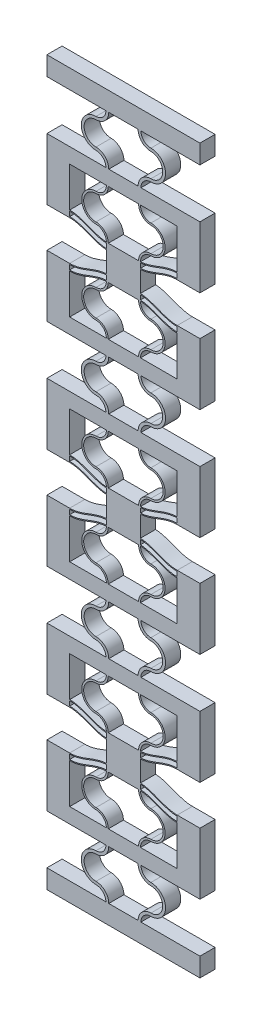
SolidWorks part; units mm, degrees
material "ABS"
ref_plane "Front Plane" through (0, 0, 0) normal (0, 0, 1) x (1, 0, 0)
ref_plane "Top Plane" through (0, 0, 0) normal (0, 1, 0) x (1, 0, 0)
ref_plane "Right Plane" through (0, 0, 0) normal (1, 0, 0) x (0, 0, -1)
sketch "Sketch1" plane through (0, 0, 0) normal (0, 0, 1) x (1, 0, 0)
  line L4 (0, 10.5) -> (0, 0)
  line L5 (10.2, 0) -> (10.2, 13) construction
  line L6 (10.2, 13) -> (10.2, 15.9852) construction
  line L17 (9.7, 0) -> (0, 0)
  line L18 (10.7, 0) -> (20.4, 0)
  line L19 (20.4, 0) -> (20.4, 10.5)
  line L20 (10.7, 13.2452) -> (10.7, 14.4852)
  line L21 (9.7, 13.2452) -> (9.7, 14.4852)
  line L22 (10.7, 14.7452) -> (10.7, 15.9852)
  line L23 (10.7, 15.9852) -> (9.7, 15.9852)
  line L24 (9.7, 15.9852) -> (9.7, 14.7452)
  line L31 (-5, 12.26) -> (-5, -4)
  line L32 (-5, -4) -> (25.4, -4)
  line L33 (25.4, -4) -> (25.4, 12.26)
  line L34 (0, 10.76) -> (0, 12)
  line L36 (-5, 12.26) -> (0, 12.26)
  line L37 (25.4, 12.26) -> (20.4, 12.26)
  line L38 (20.4, 10.76) -> (20.4, 12)
  arc A0 (10.2, 13) -> (6.95, 9.75) centre (6.95, 13) cw
  arc A1 (6.95, 9.75) -> (6.95, 3.25) centre (6.95, 6.5) ccw
  arc A2 (6.95, 3.25) -> (10.2, 0) centre (6.95, 0) cw
  arc A3 (9.7, 12.9852) -> (6.95, 10.25) centre (6.95, 13) cw
  arc A4 (6.95, 10.25) -> (6.95, 2.75) centre (6.95, 6.5) ccw
  arc A5 (6.95, 2.75) -> (9.7, 0) centre (6.95, 0) cw
  arc A6 (9.7, 13) -> (6.95, 10.25) centre (6.95, 13) cw construction
  arc A7 (13.45, 3.25) -> (10.2, 0) centre (13.45, 0) ccw
  arc A8 (13.45, 2.75) -> (10.7, 0) centre (13.45, 0) ccw
  arc A9 (13.45, 9.75) -> (13.45, 3.25) centre (13.45, 6.5) cw
  arc A10 (13.45, 10.25) -> (13.45, 2.75) centre (13.45, 6.5) cw
  arc A11 (10.7, 12.9852) -> (13.45, 10.25) centre (13.45, 13) ccw
  arc A12 (10.2, 13) -> (13.45, 9.75) centre (13.45, 13) ccw
  spline S0 degree 4 poles (-2.0399, 10.9987) (-1.9769, 10.9844) (-1.8506, 10.9568) (-1.6594, 10.9185) (-1.4063, 10.8738) (-1.1473, 10.836) (-0.8994, 10.8056) (-0.6275, 10.7825) (-0.4084, 10.7671) (-0.0945, 10.7598) (0.0489, 10.7593) (0.3554, 10.7653) (0.5833, 10.7785) (0.8327, 10.7992) (1.1232, 10.8326) (1.4148, 10.8743) (1.7521, 10.9345) (2.2064, 11.0333) (2.726, 11.1697) (3.2397, 11.3281) (3.7479, 11.5024) (4.1845, 11.6613) (4.5513, 11.7992) (4.9172, 11.9395) (5.2828, 12.0805) (5.7402, 12.2559) (6.427, 12.5125) (7.2136, 12.7819) (8.1107, 13.0284) (9.0261, 13.1932) (9.8075, 13.2661) (10.5925, 13.2661) (11.3739, 13.1932) (12.2893, 13.0284) (13.1864, 12.7819) (13.973, 12.5125) (14.6598, 12.2559) (15.2087, 12.0455) (15.6656, 11.8688) (16.1235, 11.6948) (16.6521, 11.5024) (17.1603, 11.3281) (17.6739, 11.1697) (18.1937, 11.0333) (18.5999, 10.9449) (18.8889, 10.8915) (19.1309, 10.8534) (19.3251, 10.827) (19.5196, 10.8048) (19.7158, 10.7868) (19.909, 10.7733) (20.1017, 10.7642) (20.3513, 10.7593) (20.4943, 10.7598) (20.8085, 10.7671) (21.0274, 10.7825) (21.2994, 10.8056) (21.5473, 10.836) (21.8063, 10.8738) (22.0594, 10.9185) (22.2506, 10.9568) (22.3769, 10.9844) (22.4399, 10.9987) knots 0 0 0 0 0 0.010251 0.020502 0.030753 0.041005 0.05113 0.061255 0.071381 0.081506 0.089265 0.097024 0.112543 0.120302 0.128061 0.143579 0.159098 0.174616 0.201648 0.22868 0.244198 0.259716 0.275235 0.290753 0.306271 0.32179 0.352826 0.40689 0.437927 0.468963 0.5 0.531037 0.562073 0.59311 0.647174 0.67821 0.693729 0.709247 0.740284 0.755802 0.77132 0.798352 0.825384 0.840902 0.856421 0.86418 0.871939 0.879698 0.887457 0.895217 0.902976 0.910735 0.918494 0.928619 0.938745 0.94887 0.958995 0.969247 0.979498 0.989749 1 1 1 1 1 construction
  spline S1 degree 4 poles (0, 10.76) (0.041, 10.76) (0.1243, 10.7608) (0.3554, 10.7653) (0.5833, 10.7785) (0.8327, 10.7992) (1.1232, 10.8326) (1.4148, 10.8743) (1.7521, 10.9345) (2.2064, 11.0333) (2.726, 11.1697) (3.2397, 11.3281) (3.7479, 11.5024) (4.1845, 11.6613) (4.5513, 11.7992) (4.9172, 11.9395) (5.2828, 12.0805) (5.7402, 12.2559) (6.427, 12.5125) (7.2136, 12.7819) (8.1107, 13.0284) (9.0261, 13.1932) (9.8075, 13.2661) (10.5925, 13.2661) (11.3739, 13.1932) (12.2893, 13.0284) (13.1864, 12.7819) (13.973, 12.5125) (14.6598, 12.2559) (15.2087, 12.0455) (15.6656, 11.8688) (16.1235, 11.6948) (16.6521, 11.5024) (17.1603, 11.3281) (17.6739, 11.1697) (18.1937, 11.0333) (18.5999, 10.9449) (18.8889, 10.8915) (19.1309, 10.8534) (19.3251, 10.827) (19.5196, 10.8048) (19.7158, 10.7868) (19.909, 10.7733) (20.1017, 10.7642) (20.2757, 10.7608) (20.359, 10.76) (20.4, 10.76) knots 0.081506 0.081506 0.081506 0.081506 0.081506 0.089265 0.097024 0.112543 0.120302 0.128061 0.143579 0.159098 0.174616 0.201648 0.22868 0.244198 0.259716 0.275235 0.290753 0.306271 0.32179 0.352826 0.40689 0.437927 0.468963 0.5 0.531037 0.562073 0.59311 0.647174 0.67821 0.693729 0.709247 0.740284 0.755802 0.77132 0.798352 0.825384 0.840902 0.856421 0.86418 0.871939 0.879698 0.887457 0.895217 0.902976 0.910735 0.918494 0.918494 0.918494 0.918494 0.918494
  spline S2 degree 4 poles (-2.0399, 12.2387) (-1.9769, 12.2244) (-1.8506, 12.1968) (-1.6594, 12.1585) (-1.4063, 12.1138) (-1.1473, 12.076) (-0.8994, 12.0456) (-0.6275, 12.0225) (-0.4084, 12.0071) (-0.0945, 11.9998) (0.0489, 11.9993) (0.3554, 12.0053) (0.5833, 12.0185) (0.8327, 12.0392) (1.1232, 12.0726) (1.4148, 12.1143) (1.7521, 12.1745) (2.2064, 12.2733) (2.726, 12.4097) (3.2397, 12.5681) (3.7479, 12.7424) (4.1845, 12.9013) (4.5513, 13.0392) (4.9172, 13.1795) (5.2828, 13.3205) (5.7402, 13.4959) (6.427, 13.7525) (7.2136, 14.0219) (8.1107, 14.2684) (9.0261, 14.4332) (9.8075, 14.5061) (10.5925, 14.5061) (11.3739, 14.4332) (12.2893, 14.2684) (13.1864, 14.0219) (13.973, 13.7525) (14.6598, 13.4959) (15.2087, 13.2855) (15.6656, 13.1088) (16.1235, 12.9348) (16.6521, 12.7424) (17.1603, 12.5681) (17.6739, 12.4097) (18.1937, 12.2733) (18.5999, 12.1849) (18.8889, 12.1315) (19.1309, 12.0934) (19.3251, 12.067) (19.5196, 12.0448) (19.7158, 12.0268) (19.909, 12.0133) (20.1017, 12.0042) (20.3513, 11.9993) (20.4943, 11.9998) (20.8085, 12.0071) (21.0274, 12.0225) (21.2994, 12.0456) (21.5473, 12.076) (21.8063, 12.1138) (22.0594, 12.1585) (22.2506, 12.1968) (22.3769, 12.2244) (22.4399, 12.2387) knots 0 0 0 0 0 0.010251 0.020502 0.030753 0.041005 0.05113 0.061255 0.071381 0.081506 0.089265 0.097024 0.112543 0.120302 0.128061 0.143579 0.159098 0.174616 0.201648 0.22868 0.244198 0.259716 0.275235 0.290753 0.306271 0.32179 0.352826 0.40689 0.437927 0.468963 0.5 0.531037 0.562073 0.59311 0.647174 0.67821 0.693729 0.709247 0.740284 0.755802 0.77132 0.798352 0.825384 0.840902 0.856421 0.86418 0.871939 0.879698 0.887457 0.895217 0.902976 0.910735 0.918494 0.928619 0.938745 0.94887 0.958995 0.969247 0.979498 0.989749 1 1 1 1 1 construction
  spline S3 degree 4 poles (0, 12) (0.041, 12) (0.1243, 12.0008) (0.3554, 12.0053) (0.5833, 12.0185) (0.8327, 12.0392) (1.1232, 12.0726) (1.4148, 12.1143) (1.7521, 12.1745) (2.2064, 12.2733) (2.726, 12.4097) (3.2397, 12.5681) (3.7479, 12.7424) (4.1845, 12.9013) (4.5513, 13.0392) (4.9172, 13.1795) (5.2828, 13.3205) (5.7402, 13.4959) (6.427, 13.7525) (7.2136, 14.0219) (8.1107, 14.2684) (9.0261, 14.4332) (9.8075, 14.5061) (10.5925, 14.5061) (11.3739, 14.4332) (12.2893, 14.2684) (13.1864, 14.0219) (13.973, 13.7525) (14.6598, 13.4959) (15.2087, 13.2855) (15.6656, 13.1088) (16.1235, 12.9348) (16.6521, 12.7424) (17.1603, 12.5681) (17.6739, 12.4097) (18.1937, 12.2733) (18.5999, 12.1849) (18.8889, 12.1315) (19.1309, 12.0934) (19.3251, 12.067) (19.5196, 12.0448) (19.7158, 12.0268) (19.909, 12.0133) (20.1017, 12.0042) (20.2757, 12.0008) (20.359, 12) (20.4, 12) knots 0.081506 0.081506 0.081506 0.081506 0.081506 0.089265 0.097024 0.112543 0.120302 0.128061 0.143579 0.159098 0.174616 0.201648 0.22868 0.244198 0.259716 0.275235 0.290753 0.306271 0.32179 0.352826 0.40689 0.437927 0.468963 0.5 0.531037 0.562073 0.59311 0.647174 0.67821 0.693729 0.709247 0.740284 0.755802 0.77132 0.798352 0.825384 0.840902 0.856421 0.86418 0.871939 0.879698 0.887457 0.895217 0.902976 0.910735 0.918494 0.918494 0.918494 0.918494 0.918494
  spline S4 degree 4 poles (-2.0399, 12.4987) (-1.9769, 12.4844) (-1.8506, 12.4568) (-1.6594, 12.4185) (-1.4063, 12.3738) (-1.1473, 12.336) (-0.8994, 12.3056) (-0.6275, 12.2825) (-0.4084, 12.2671) (-0.0945, 12.2598) (0.0489, 12.2593) (0.3554, 12.2653) (0.5833, 12.2785) (0.8327, 12.2992) (1.1232, 12.3326) (1.4148, 12.3743) (1.7521, 12.4345) (2.2064, 12.5333) (2.726, 12.6697) (3.2397, 12.8281) (3.7479, 13.0024) (4.1845, 13.1613) (4.5513, 13.2992) (4.9172, 13.4395) (5.2828, 13.5805) (5.7402, 13.7559) (6.427, 14.0125) (7.2136, 14.2819) (8.1107, 14.5284) (9.0261, 14.6932) (9.8075, 14.7661) (10.5925, 14.7661) (11.3739, 14.6932) (12.2893, 14.5284) (13.1864, 14.2819) (13.973, 14.0125) (14.6598, 13.7559) (15.2087, 13.5455) (15.6656, 13.3688) (16.1235, 13.1948) (16.6521, 13.0024) (17.1603, 12.8281) (17.6739, 12.6697) (18.1937, 12.5333) (18.5999, 12.4449) (18.8889, 12.3915) (19.1309, 12.3534) (19.3251, 12.327) (19.5196, 12.3048) (19.7158, 12.2868) (19.909, 12.2733) (20.1017, 12.2642) (20.3513, 12.2593) (20.4943, 12.2598) (20.8085, 12.2671) (21.0274, 12.2825) (21.2994, 12.3056) (21.5473, 12.336) (21.8063, 12.3738) (22.0594, 12.4185) (22.2506, 12.4568) (22.3769, 12.4844) (22.4399, 12.4987) knots 0 0 0 0 0 0.010251 0.020502 0.030753 0.041005 0.05113 0.061255 0.071381 0.081506 0.089265 0.097024 0.112543 0.120302 0.128061 0.143579 0.159098 0.174616 0.201648 0.22868 0.244198 0.259716 0.275235 0.290753 0.306271 0.32179 0.352826 0.40689 0.437927 0.468963 0.5 0.531037 0.562073 0.59311 0.647174 0.67821 0.693729 0.709247 0.740284 0.755802 0.77132 0.798352 0.825384 0.840902 0.856421 0.86418 0.871939 0.879698 0.887457 0.895217 0.902976 0.910735 0.918494 0.928619 0.938745 0.94887 0.958995 0.969247 0.979498 0.989749 1 1 1 1 1 construction
  spline S5 degree 4 poles (0, 12.26) (0.041, 12.26) (0.1243, 12.2608) (0.3554, 12.2653) (0.5833, 12.2785) (0.8327, 12.2992) (1.1232, 12.3326) (1.4148, 12.3743) (1.7521, 12.4345) (2.2064, 12.5333) (2.726, 12.6697) (3.2397, 12.8281) (3.7479, 13.0024) (4.1845, 13.1613) (4.5513, 13.2992) (4.9172, 13.4395) (5.2828, 13.5805) (5.7402, 13.7559) (6.427, 14.0125) (7.2136, 14.2819) (8.1107, 14.5284) (9.0261, 14.6932) (9.8075, 14.7661) (10.5925, 14.7661) (11.3739, 14.6932) (12.2893, 14.5284) (13.1864, 14.2819) (13.973, 14.0125) (14.6598, 13.7559) (15.2087, 13.5455) (15.6656, 13.3688) (16.1235, 13.1948) (16.6521, 13.0024) (17.1603, 12.8281) (17.6739, 12.6697) (18.1937, 12.5333) (18.5999, 12.4449) (18.8889, 12.3915) (19.1309, 12.3534) (19.3251, 12.327) (19.5196, 12.3048) (19.7158, 12.2868) (19.909, 12.2733) (20.1017, 12.2642) (20.2757, 12.2608) (20.359, 12.26) (20.4, 12.26) knots 0.081506 0.081506 0.081506 0.081506 0.081506 0.089265 0.097024 0.112543 0.120302 0.128061 0.143579 0.159098 0.174616 0.201648 0.22868 0.244198 0.259716 0.275235 0.290753 0.306271 0.32179 0.352826 0.40689 0.437927 0.468963 0.5 0.531037 0.562073 0.59311 0.647174 0.67821 0.693729 0.709247 0.740284 0.755802 0.77132 0.798352 0.825384 0.840902 0.856421 0.86418 0.871939 0.879698 0.887457 0.895217 0.902976 0.910735 0.918494 0.918494 0.918494 0.918494 0.918494
  spline S8 degree 4 poles (-2.0399, 10.7387) (-1.9769, 10.7244) (-1.8506, 10.6968) (-1.6594, 10.6585) (-1.4063, 10.6138) (-1.1473, 10.576) (-0.8994, 10.5456) (-0.6275, 10.5225) (-0.4084, 10.5071) (-0.0945, 10.4998) (0.0489, 10.4993) (0.3554, 10.5053) (0.5833, 10.5185) (0.8327, 10.5392) (1.1232, 10.5726) (1.4148, 10.6143) (1.7521, 10.6745) (2.2064, 10.7733) (2.726, 10.9097) (3.2397, 11.0681) (3.7479, 11.2424) (4.1845, 11.4013) (4.5513, 11.5392) (4.9172, 11.6795) (5.2828, 11.8205) (5.7402, 11.9959) (6.427, 12.2525) (7.2136, 12.5219) (8.1107, 12.7684) (9.0261, 12.9332) (9.8075, 13.0061) (10.5925, 13.0061) (11.3739, 12.9332) (12.2893, 12.7684) (13.1864, 12.5219) (13.973, 12.2525) (14.6598, 11.9959) (15.2087, 11.7855) (15.6656, 11.6088) (16.1235, 11.4348) (16.6521, 11.2424) (17.1603, 11.0681) (17.6739, 10.9097) (18.1937, 10.7733) (18.5999, 10.6849) (18.8889, 10.6315) (19.1309, 10.5934) (19.3251, 10.567) (19.5196, 10.5448) (19.7158, 10.5268) (19.909, 10.5133) (20.1017, 10.5042) (20.3513, 10.4993) (20.4943, 10.4998) (20.8085, 10.5071) (21.0274, 10.5225) (21.2994, 10.5456) (21.5473, 10.576) (21.8063, 10.6138) (22.0594, 10.6585) (22.2506, 10.6968) (22.3769, 10.7244) (22.4399, 10.7387) knots 0 0 0 0 0 0.010251 0.020502 0.030753 0.041005 0.05113 0.061255 0.071381 0.081506 0.089265 0.097024 0.112543 0.120302 0.128061 0.143579 0.159098 0.174616 0.201648 0.22868 0.244198 0.259716 0.275235 0.290753 0.306271 0.32179 0.352826 0.40689 0.437927 0.468963 0.5 0.531037 0.562073 0.59311 0.647174 0.67821 0.693729 0.709247 0.740284 0.755802 0.77132 0.798352 0.825384 0.840902 0.856421 0.86418 0.871939 0.879698 0.887457 0.895217 0.902976 0.910735 0.918494 0.928619 0.938745 0.94887 0.958995 0.969247 0.979498 0.989749 1 1 1 1 1 construction
  spline S9 degree 4 poles (0, 10.5) (0.041, 10.5) (0.1243, 10.5008) (0.3554, 10.5053) (0.5833, 10.5185) (0.8327, 10.5392) (1.1232, 10.5726) (1.4148, 10.6143) (1.7521, 10.6745) (2.2064, 10.7733) (2.726, 10.9097) (3.2397, 11.0681) (3.7479, 11.2424) (4.1845, 11.4013) (4.5513, 11.5392) (4.9172, 11.6795) (5.2828, 11.8205) (5.7402, 11.9959) (6.427, 12.2525) (7.2136, 12.5219) (8.1107, 12.7684) (9.0261, 12.9332) (9.8075, 13.0061) (10.5925, 13.0061) (11.3739, 12.9332) (12.2893, 12.7684) (13.1864, 12.5219) (13.973, 12.2525) (14.6598, 11.9959) (15.2087, 11.7855) (15.6656, 11.6088) (16.1235, 11.4348) (16.6521, 11.2424) (17.1603, 11.0681) (17.6739, 10.9097) (18.1937, 10.7733) (18.5999, 10.6849) (18.8889, 10.6315) (19.1309, 10.5934) (19.3251, 10.567) (19.5196, 10.5448) (19.7158, 10.5268) (19.909, 10.5133) (20.1017, 10.5042) (20.2757, 10.5008) (20.359, 10.5) (20.4, 10.5) knots 0.081506 0.081506 0.081506 0.081506 0.081506 0.089265 0.097024 0.112543 0.120302 0.128061 0.143579 0.159098 0.174616 0.201648 0.22868 0.244198 0.259716 0.275235 0.290753 0.306271 0.32179 0.352826 0.40689 0.437927 0.468963 0.5 0.531037 0.562073 0.59311 0.647174 0.67821 0.693729 0.709247 0.740284 0.755802 0.77132 0.798352 0.825384 0.840902 0.856421 0.86418 0.871939 0.879698 0.887457 0.895217 0.902976 0.910735 0.918494 0.918494 0.918494 0.918494 0.918494
  dimension "D4" = 0.26
  dimension "D6" = 4
  dimension "D1" = 13
  dimension "D2" = 0.5
  dimension "D3" = 0.26
  dimension "D7" = 5
  dimension "D5" = 1.5
extrude "Boss-Extrude1" add sketch "Sketch1" along normal blind 4
sketch "Sketch4" plane through (0, 15.9852, 0) normal (0, 1, 0) x (1, 0, 0)
  line L24 (10.7, 0) -> (9.7, 0)
  line L25 (9.7, 0) -> (9.7, -4)
  line L26 (10.7, 0) -> (9.7, 0)
  line L27 (10.7, -4) -> (10.7, 0)
  line L29 (9.7, 0) -> (9.7, -4)
  line L31 (10.7, -4) -> (10.7, 0)
  line L32 (9.7, -4) -> (10.7, -4)
  line L33 (9.7, -4) -> (10.7, -4)
  dimension "D1" = 0
extrude "Boss-Extrude2" add sketch "Sketch4" along normal blind 1.5
mirror "Mirror3" about plane through (0, 17.4852, 0) normal (0, 1, 0) of bodies 179
ref_plane "Plane1" through (10.2, 0, 0) normal (-1, 0, 0) x (0, 0, 1)
split "Split2" trim tools "Plane1" bodies to split 247 102 resulting bodies 225
sketch "Sketch7" plane through (10.2, 0, 0) normal (-1, 0, 0) x (0, 0, 1)
  line L4 (4, 34.9704) -> (4, 38.9704)
  line L12 (0, 13) -> (4, 13)
  line L13 (0, 13) -> (4, 13)
  line L14 (4, 13) -> (4, 21.9704)
  line L15 (4, 13) -> (4, 21.9704)
  line L20 (4, 0) -> (0, 0)
  line L22 (4, 0) -> (0, 0)
  line L23 (0, -4) -> (4, -4)
  line L27 (0, -4) -> (4, -4)
  line L31 (4, 21.9704) -> (0, 21.9704)
  line L32 (4, 21.9704) -> (0, 21.9704)
  line L33 (0, 21.9704) -> (0, 13)
  line L34 (0, 21.9704) -> (0, 13)
  line L36 (4, -4) -> (4, 0)
  line L38 (4, 34.9704) -> (4, 38.9704)
  line L39 (4, 34.9704) -> (4, 38.9704)
  line L40 (4, 38.9704) -> (0, 38.9704)
  line L41 (4, 38.9704) -> (0, 38.9704)
  line L46 (4, 34.9704) -> (4, 38.9704)
  line L51 (0, 38.9704) -> (0, 34.9704)
  line L52 (0, 38.9704) -> (0, 34.9704)
  line L53 (0, 34.9704) -> (4, 34.9704)
  line L54 (0, 34.9704) -> (4, 34.9704)
  line L55 (4, 38.9704) -> (0, 38.9704)
  line L57 (4, 38.9704) -> (0, 38.9704)
  line L59 (4, -4) -> (4, 0)
  line L60 (0, 0) -> (0, -4)
  line L61 (0, 0) -> (0, -4)
  line L62 (0, 38.9704) -> (0, 34.9704)
  line L63 (0, 38.9704) -> (0, 34.9704)
  line L64 (0, 34.9704) -> (4, 34.9704)
  line L65 (0, 34.9704) -> (4, 34.9704)
  dimension "D1" = 0
  dimension "D2" = 0
  dimension "D3" = 0
  dimension "D4" = 0
extrude "Boss-Extrude3" add sketch "Sketch7" along normal blind 4
mirror "Mirror2" about plane through (6.2, 0, 0) normal (-1, 0, 0) of bodies 226
other "Move Face1" face at (-13, 30.8404, 2) face at (-13, 4.13, 2) face at (25.4, 4.13, 2) face at (25.4, 30.8404, 2) parameters "D1"=1
sketch "Sketch8" plane through (0, 0, 4) normal (0, 0, 1) x (1, 0, 0)
  line L0 (10.2, 13) -> (10.2, 0) construction
  line L1 (10.2, 0) -> (10.2, -4) construction
  line L2 (-14, -4) -> (26.4, -4) construction
  line L3 (10.2, -17) -> (10.7, -17)
  line L4 (10.7, -4) -> (10.2, -4)
  arc A0 (13.45, 2.75) -> (10.7, 0) centre (13.45, 0) ccw construction
  arc A1 (13.45, 3.25) -> (10.2, 0) centre (13.45, 0) ccw construction
  arc A2 (13.45, 3.25) -> (13.45, 9.75) centre (13.45, 6.5) ccw construction
  arc A3 (13.45, 2.75) -> (13.45, 10.25) centre (13.45, 6.5) ccw construction
  arc A4 (10.2, 13) -> (13.45, 9.75) centre (13.45, 13) ccw construction
  arc A5 (10.7, 12.9852) -> (13.45, 10.25) centre (13.45, 13) ccw construction
  arc A6 (13.45, 2.75) -> (10.7, 0) centre (13.45, 0) ccw
  arc A7 (13.45, 3.25) -> (10.2, 0) centre (13.45, 0) ccw
  arc A8 (13.45, 3.25) -> (13.45, 9.75) centre (13.45, 6.5) ccw
  arc A9 (13.45, 2.75) -> (13.45, 10.25) centre (13.45, 6.5) ccw
  arc A10 (10.2, 13) -> (13.45, 9.75) centre (13.45, 13) ccw
  arc A11 (10.7, 12.9852) -> (13.45, 10.25) centre (13.45, 13) ccw
  arc A12 (13.45, -13.75) -> (13.45, -7.25) centre (13.45, -10.5) ccw
  arc A13 (13.45, -13.75) -> (10.2, -17) centre (13.45, -17) ccw
  arc A14 (10.7, -4) -> (13.45, -6.75) centre (13.45, -4) ccw
  arc A15 (13.45, -14.25) -> (10.7, -17) centre (13.45, -17) ccw
  arc A16 (13.45, -14.25) -> (13.45, -6.75) centre (13.45, -10.5) ccw
  arc A17 (10.2, -4) -> (13.45, -7.25) centre (13.45, -4) ccw
  dimension "D1" = 13
  dimension "D2" = 13
  dimension "D3" = 6.5
extrude "Boss-Extrude4" add sketch "Sketch8" against normal up to surface (4 mm away) separate body contours A12 A17 L4 A14 A16 A15 L3 A13 up to face at (6.2, 17.4852, 0)
other "Move Face2" face at (11.7902, -5.6598, 2) face at (15.325, -10.5, 2) face at (11.7902, -15.3402, 2) face at (11.4885, -15.0385, 2) face at (15.075, -10.5, 2) face at (11.4885, -5.9615, 2) parameters "D1"=0.125
ref_plane "Plane2" through (6.2, 0, 0) normal (1, 0, 0) x (0, 0, -1)
mirror "Mirror5" about plane through (6.2, 0, 0) normal (1, 0, 0) of bodies 294 283
pattern_linear "LPattern2" count 2 spacing 55.9704 along (0, 1, 0) of bodies 294 288 283
combine bodies "Combine2" operation type add bodies to combine 293 288 294
pattern_linear "LPattern1" count 3 spacing 55.9704 along (0, 1, 0)
combine bodies "Combine1" operation type add bodies to combine 291 285 286 289 290
sketch "Sketch12" plane through (0, 0, 4) normal (0, 0, 1) x (1, 0, 0)
  line L0 (26.4, 38.9704) -> (26.4, 22.7104) construction
  line L1 (-14, 56.9704) -> (26.4, 56.9704)
  line L2 (-14, 56.9704) -> (-14, 51.9704)
  line L3 (-14, 51.9704) -> (26.4, 51.9704)
  line L4 (26.4, 56.9704) -> (26.4, 51.9704)
  line L5 (-14, 38.9704) -> (-14, 22.7104) construction
  line L7 (-14, -115.9408) -> (-14, -99.6808) construction
  line L8 (-14, -128.9408) -> (26.4, -128.9408)
  line L9 (-14, -128.9408) -> (-14, -133.9408)
  line L10 (-14, -133.9408) -> (26.4, -133.9408)
  line L11 (26.4, -128.9408) -> (26.4, -133.9408)
  line L12 (26.4, -115.9408) -> (26.4, -99.6808) construction
  dimension "D1" = 5
extrude "Boss-Extrude5" add sketch "Sketch12" against normal up to surface (4 mm away) contours L4 L1 L2 L3 | L8 L11 L10 L9
